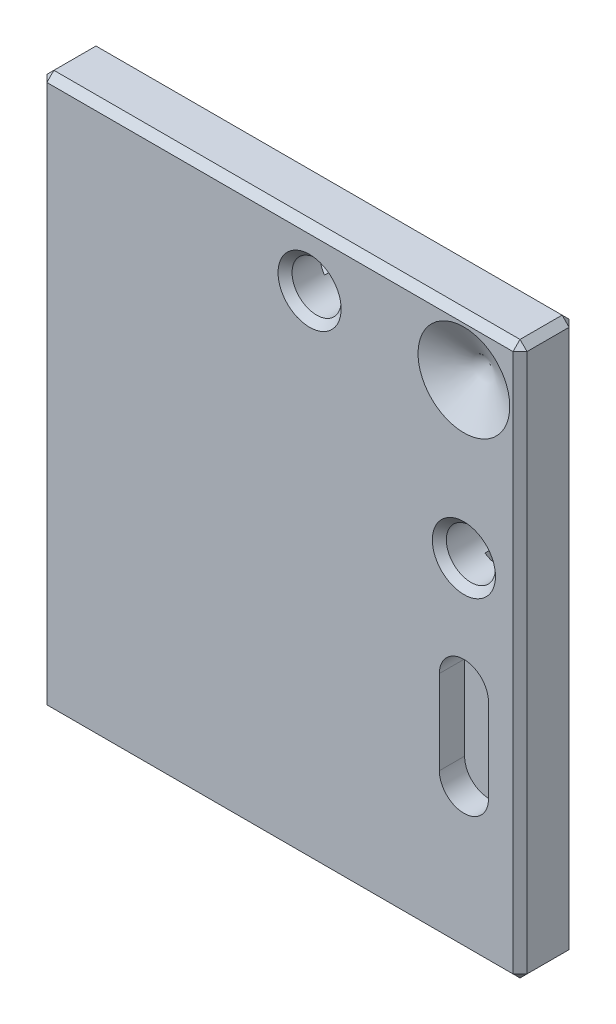
SolidWorks part; units mm, degrees
material "3.1645 (EN-AW 2030)"
ref_plane "Přední rovina" through (0, 0, 0) normal (0, 0, 1) x (1, 0, 0)
ref_plane "Horní rovina" through (0, 0, 0) normal (0, 1, 0) x (1, 0, 0)
ref_plane "Pravá rovina" through (0, 0, 0) normal (1, 0, 0) x (0, 0, -1)
sketch "Skica1" plane through (0, 0, 0) normal (0, 0, 1) x (1, 0, 0)
  line L0 (0, 22.0599) -> (0, -9.3599) construction
  line L1 (0, 6.35) -> (-11.1125, 6.35) construction
  line L2 (-17.1125, 28.0599) -> (17.1125, 28.0599)
  line L3 (-17.1125, 28.0599) -> (-17.1125, -11.3599)
  line L4 (-17.1125, -11.3599) -> (17.1125, -11.3599)
  line L5 (17.1125, 28.0599) -> (17.1125, -11.3599)
  line L6 (0, 6.35) -> (11.1125, 6.35) construction
  line L7 (0, 28.0599) -> (0, 22.0599) construction
  spline S0 degree 3 poles (0, -15.7099) (-22.225, -15.7099) (-22.225, 15.7099) (0, 15.7099) knots 3.141593 3.141593 3.141593 3.141593 6.283185 6.283185 6.283185 6.283185 weights 1 0.333333 0.333333 1 construction
  spline S1 degree 3 poles (0, -15.7099) (-22.225, -15.7099) (-22.225, 15.7099) (0, 15.7099) knots 3.141593 3.141593 3.141593 3.141593 6.283185 6.283185 6.283185 6.283185 weights 1 0.333333 0.333333 1 construction
  spline S2 degree 3 poles (0, -9.3599) (22.225, -9.3599) (22.225, 22.0599) (0, 22.0599) knots 0 0 0 0 3.141593 3.141593 3.141593 3.141593 weights 1 0.333333 0.333333 1
  spline S3 degree 3 poles (0, 22.0599) (-22.225, 22.0599) (-22.225, -9.3599) (0, -9.3599) knots 3.141593 3.141593 3.141593 3.141593 6.283185 6.283185 6.283185 6.283185 weights 1 0.333333 0.333333 1
  spline S4 degree 3 poles (0, -9.3599) (22.225, -9.3599) (22.225, 22.0599) (0, 22.0599) knots 0 0 0 0 3.141593 3.141593 3.141593 3.141593 weights 1 0.333333 0.333333 1 construction
  spline S5 degree 3 poles (0, 22.0599) (-22.225, 22.0599) (-22.225, -9.3599) (0, -9.3599) knots 3.141593 3.141593 3.141593 3.141593 6.283185 6.283185 6.283185 6.283185 weights 1 0.333333 0.333333 1 construction
  spline S6 degree 1 poles (0, 22.3099) (0, -9.6099) knots 0 0 1 1 construction
  spline S7 degree 1 poles (0, -9.6099) (0, 22.3099) knots 0 0 1 1 construction
  spline S8 degree 3 poles (0, 22.3099) (-0.2466, 22.3099) (-0.7281, 22.2888) (-1.7776, 22.1456) (-3.185, 21.7431) (-5.0047, 20.7772) (-7.4843, 18.6887) (-9.7835, 15.1436) (-11.1249, 10.32) (-11.4813, 6.35) (-11.1249, 2.38) (-9.7835, -2.4436) (-7.4843, -5.9887) (-5.0047, -8.0772) (-3.185, -9.0431) (-1.7776, -9.4456) (-0.7281, -9.5888) (-0.2466, -9.6099) (0, -9.6099) knots 3.141593 3.141593 3.141593 3.141593 3.239767 3.337942 3.534292 3.730641 3.926991 4.31969 4.516039 4.712389 4.908739 5.105088 5.497787 5.694137 5.890486 6.086836 6.185011 6.283185 6.283185 6.283185 6.283185
  spline S9 degree 3 poles (0, -9.6099) (0.2466, -9.6099) (0.7281, -9.5888) (1.7776, -9.4456) (3.185, -9.0431) (5.0047, -8.0772) (7.4843, -5.9887) (9.7835, -2.4436) (11.1249, 2.38) (11.4813, 6.35) (11.1249, 10.32) (9.7835, 15.1436) (7.4843, 18.6887) (5.0047, 20.7772) (3.185, 21.7431) (1.7776, 22.1456) (0.7281, 22.2888) (0.2466, 22.3099) (0, 22.3099) knots 0 0 0 0 0.098175 0.19635 0.392699 0.589049 0.785398 1.178097 1.374447 1.570796 1.767146 1.963495 2.356194 2.552544 2.748894 2.945243 3.043418 3.141593 3.141593 3.141593 3.141593
  dimension "D2" = 6
  dimension "D4" = 6
  dimension "D5" = 2
  dimension "D1" = 0
  dimension "D6" = 0.25
extrude "Přidat vysunutím1" add sketch "Skica1" against normal blind 0.5 contours S4 S5 | L3 L2 L5 L4
sketch "Skica2" plane through (0, 0, 0) normal (0, 0, 1) x (1, 0, 0)
  line L4 (-17.1125, -11.3599) -> (17.1125, -11.3599)
  line L5 (17.1125, -11.3599) -> (17.1125, 28.0599)
  line L6 (17.1125, 28.0599) -> (-17.1125, 28.0599)
  line L7 (-17.1125, 28.0599) -> (-17.1125, -11.3599)
  line L8 (-17.1125, -11.3599) -> (17.1125, -11.3599)
  line L9 (17.1125, -11.3599) -> (17.1125, 28.0599)
  line L10 (17.1125, 28.0599) -> (-17.1125, 28.0599)
  line L11 (-17.1125, 28.0599) -> (-17.1125, -11.3599)
  dimension "D1" = 0
extrude "Přidat vysunutím2" add sketch "Skica2" along direction (0, 0, 1) on the side of the normal blind 3.5
sketch "Skica3" plane through (0, 0, 3.5) normal (0, 0, 1) x (1, 0, 0)
  line L0 (13.1125, 24.0599) -> (-8.8875, 24.0599) construction
  line L1 (13.1125, 24.0599) -> (13.1125, 2.0599) construction
  line L2 (17.1125, 28.0599) -> (-17.1125, 28.0599) construction
  line L3 (17.1125, -11.3599) -> (17.1125, 28.0599) construction
  circle A0 centre (13.1125, 24.0599) radius 2.5 construction
  point P8 (13.1125, 13.0599)
  point P9 (2.1125, 24.0599)
  point P10 (2.1125, 24.0599)
  point P11 (13.1125, 13.0599)
  dimension "D1" = 5
  dimension "D3" = 4
  dimension "D2" = 4
  dimension "D4" = 22
sketch "Skica6" plane through (0, 0, 3.5) normal (0, 0, 1) x (1, 0, 0)
  line L0 (13.1125, -0.9401) -> (13.1125, 5.0599) construction
  line L1 (11.3625, -0.9401) -> (11.3625, 5.0599)
  line L2 (14.8625, -0.9401) -> (14.8625, 5.0599)
  arc A0 (11.3625, -0.9401) -> (14.8625, -0.9401) centre (13.1125, -0.9401) ccw
  arc A1 (14.8625, 5.0599) -> (11.3625, 5.0599) centre (13.1125, 5.0599) ccw
  point P0 (13.1125, 2.0599)
  point P4 (13.1125, 2.0599)
  dimension "D1" = 6
  dimension "D2" = 3.5
extrude "Odebrat vysunutím1" cut sketch "Skica6" against normal blind 1.8 contours L2 A1 L1 A0
ref_plane "Rovina2" through (13.1125, 0, 0) normal (-1, 0, 0) x (0, -1, 0)
sketch "Skica8" plane through (13.1125, 0, 0) normal (-1, 0, 0) x (0, -1, 0)
  line L0 (-24.0599, 3.5) -> (-24.0599, 5.5) construction
  line L1 (-24.0599, 3.5) -> (-2.0599, 3.5) construction
  line L2 (-23.1809, 5.5) -> (-24.9389, 5.5) construction
  line L3 (-21.5599, 3.5) -> (-26.5599, 3.5) construction
  line L4 (-21.5599, 3.5) -> (-26.5599, 3.5) construction
  line L5 (-26.5599, 4.5) -> (-21.5599, 4.5) construction
  line L6 (-20.792, 5.5) -> (-24.0599, 7.3868) construction
  line L7 (-24.0599, 7.3868) -> (-27.3278, 5.5) construction
  line L8 (-20.792, 3.5) -> (-24.0599, 1.6132)
  line L9 (-24.0599, 1.6132) -> (-27.3278, 3.5)
  line L12 (-27.3278, 3.5) -> (-20.792, 3.5)
  circle A0 centre (-24.0599, 4.5) radius 2.5 construction
  point P7 (-24.0599, 5.5)
  dimension "D1" = 2
  dimension "D2" = 120
sketch "Skica9" plane through (13.1125, 0, 0) normal (-1, 0, 0) x (0, -1, 0)
  line L0 (-27.3278, 3.5) -> (-20.792, 3.5) construction
  line L1 (-24.0599, 1.6132) -> (-27.3278, 3.5) construction
  line L2 (-27.3278, 3.5) -> (-24.0599, 3.5)
  line L3 (-24.0599, 1.6132) -> (-27.3278, 3.5)
  line L5 (-24.0599, 3.5) -> (-24.0599, 1.6132) construction
  line L6 (-24.0599, 1.6132) -> (-24.0599, 3.5)
revolve "Odebrat rotací1" cut sketch "Skica9" angle 360 about L5
sketch "Skica10" plane through (0, 0, 0) normal (0, 0, -1) x (-1, 0, 0)
  circle A0 centre (0, 6.35) radius 4
  point P0 (0, 6.35)
  dimension "D1" = 8
extrude "Odebrat vysunutím2" cut sketch "Skica10" against normal blind 0.3
ref_plane "Rovina3" through (0, 5.0599, 0) normal (0, -1, 0) x (0, 0, 1)
sketch "Skica11" plane through (0, 5.0599, 0) normal (0, -1, 0) x (0, 0, 1)
  line L1 (2.45, -12.2125) -> (2.45, -14.0125) construction
  line L2 (2.45, -13.1125) -> (3.5, -13.1125) construction
  line L5 (1.7, -14.8625) -> (1.7, -11.3625) construction
  line L6 (1.7, -14.8625) -> (1.7, -11.3625) construction
  dimension "D1" = 1.8
  dimension "D2" = 0.75
hole_wizard "Ø3.5 (3.5) průměr díry2" positions "3DSkica1" profile "Skica15" hole size "Ø3.5" standard "ISO"
sketch3d "3DSkica1"
  point P0 (2.1125, 24.0599, 3.5)
  point P3 (13.1125, 13.0599, 3.5)
sketch "Skica15" plane through (2.1125, 24.0599, 3.5) normal (1, 0, 0) x (0, -1, 0)
  line L0 (0, 0) -> (0, 5.0505)
  line L1 (0, 5.0505) -> (1.75, 3.999)
  line L2 (1.75, 3.999) -> (1.75, 0)
  line L5 (1.75, 0) -> (0, 0)
  line L10 (0, 5.0505) -> (-1.75, 3.999) construction
  line L11 (0, -6.35) -> (0, 107.95) construction
  dimension "Průměr díry" = 3.5
  dimension "Hloubka díry" = 3.999
  dimension "Úhel vrtání" = 118
sketch "Skica16" plane through (0, 0, -0.5) normal (0, 0, -1) x (-1, 0, 0)
  line L0 (0.3875, 24.0599) -> (-4.6125, 24.0599) construction
  line L1 (0.3875, 23.0599) -> (-4.6125, 23.0599)
  line L2 (0.3875, 25.0599) -> (-4.6125, 25.0599)
  line L3 (-13.1125, 10.5599) -> (-13.1125, 15.5599) construction
  line L4 (-14.1125, 10.5599) -> (-14.1125, 15.5599)
  line L5 (-12.1125, 10.5599) -> (-12.1125, 15.5599)
  arc A0 (0.3875, 23.0599) -> (0.3875, 25.0599) centre (0.3875, 24.0599) ccw
  arc A1 (-4.6125, 25.0599) -> (-4.6125, 23.0599) centre (-4.6125, 24.0599) ccw
  arc A2 (-14.1125, 10.5599) -> (-12.1125, 10.5599) centre (-13.1125, 10.5599) ccw
  arc A3 (-12.1125, 15.5599) -> (-14.1125, 15.5599) centre (-13.1125, 15.5599) ccw
  point P2 (-2.1125, 24.0599)
  point P10 (-13.1125, 13.0599)
  point P16 (-5.6125, 24.0599)
  point P17 (1.3875, 24.0599)
  dimension "D1" = 2
  dimension "D2" = 7
extrude "Odebrat vysunutím3" cut sketch "Skica16" against normal blind 1.5
chamfer "Zkosení1" distance 0.5 angle 45 12 edges at (0, -11.3599, -0.5) (0, -11.3599, 3.5) (0, 28.0599, 3.5) (-17.1125, 8.35, -0.5) (-17.1125, -11.3599, 1.5) (-17.1125, 8.35, 3.5) (17.1125, 8.35, 3.5) (0, 28.0599, -0.5) (-17.1125, 28.0599, 1.5) (17.1125, 8.35, -0.5) (17.1125, -11.3599, 1.5) (17.1125, 28.0599, 1.5)
chamfer "Zkosení2" distance 0.5 angle 45 2 edges at (14.8625, 13.0599, 3.5) (3.8625, 24.0599, 3.5)
